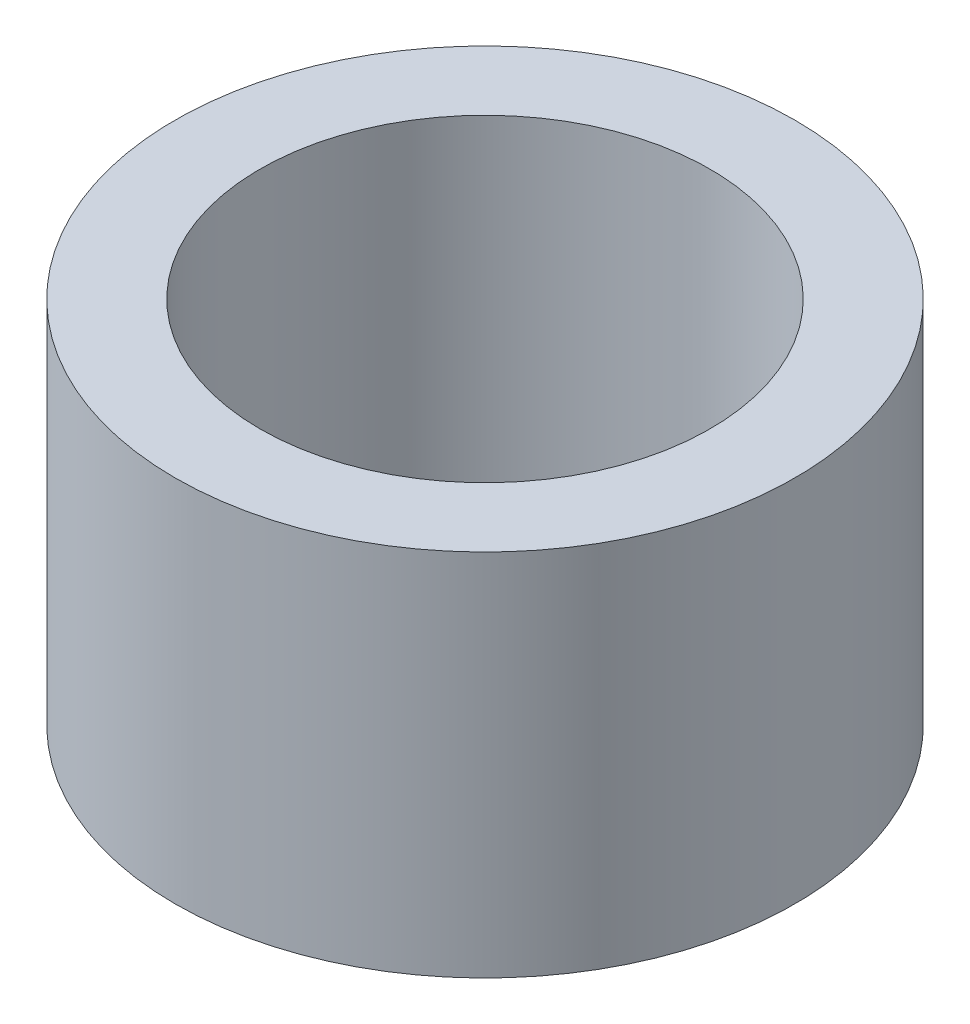
SolidWorks part; units mm, degrees
ref_plane "정면" through (0, 0, 0) normal (0, 0, 1) x (1, 0, 0)
ref_plane "윗면" through (0, 0, 0) normal (0, 1, 0) x (1, 0, 0)
ref_plane "우측면" through (0, 0, 0) normal (1, 0, 0) x (0, 0, -1)
sketch "스케치1" plane through (0, 0, 0) normal (0, 1, 0) x (1, 0, 0)
  circle A0 centre (0, 0) radius 8.4
  circle A1 centre (0, 0) radius 6.1
  dimension "D1" = 16.8
  dimension "D2" = 12.2
extrude "보스-돌출1" add sketch "스케치1" along normal mid plane 10
